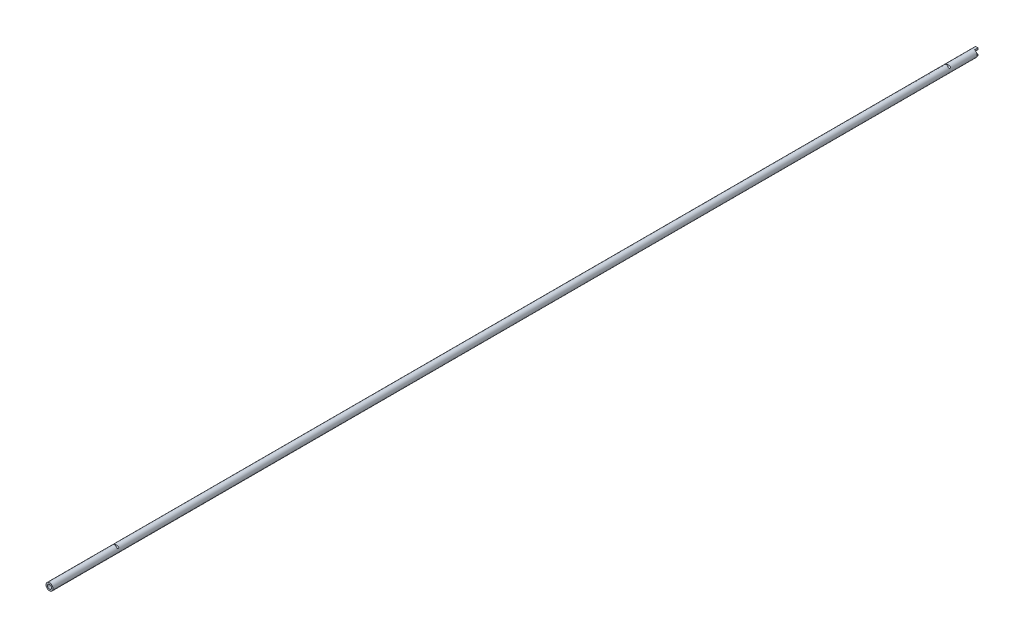
SolidWorks part; units mm, degrees
ref_plane "Front Plane" through (0, 0, 0) normal (0, 0, 1) x (1, 0, 0)
ref_plane "Top Plane" through (0, 0, 0) normal (0, 1, 0) x (1, 0, 0)
ref_plane "Right Plane" through (0, 0, 0) normal (1, 0, 0) x (0, 0, -1)
sketch "Sketch1" plane through (0, 0, 0) normal (0, 0, 1) x (1, 0, 0)
  circle A0 centre (0, 0) radius 1.98
  circle A1 centre (0, 0) radius 1.125
extrude "Extrude1" add sketch "Sketch1" along normal blind 522
sketch "Sketch2" plane through (0, 0, 0) normal (1, 0, 0) x (0, 0, -1)
  line L1 (-522, 1.98) -> (-522, -1.98) construction
  circle A0 centre (-485, 1.5) radius 0.5
  circle A1 centre (-17, 1.5) radius 0.5
  point P2 (-17, 1.5)
  dimension "D1" = 37
  dimension "D2" = 1.5
  dimension "D3" = 17
  dimension "D4" = 1.5
extrude "Extrude2" cut sketch "Sketch2" against normal through all and the other way through all
sketch "Sketch3" plane through (0, 0, 0) normal (0, 0, 1) x (1, 0, 0)
  line L0 (0.5, -3) -> (0.5, 3)
  line L1 (0.5, 3) -> (3.1984, 3)
  line L2 (0.5, -3) -> (3.1984, -3)
  line L3 (3.1984, -3) -> (3.1984, 3)
  point P0 (0, 0)
extrude "Extrude5" cut sketch "Sketch3" along normal blind 2
